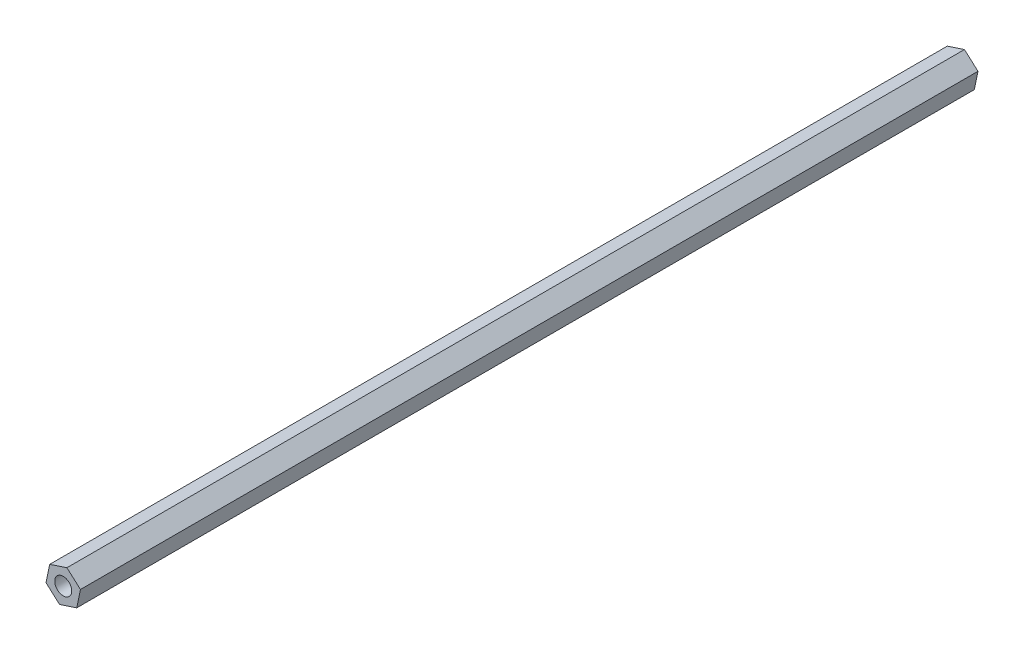
SolidWorks part; units mm, degrees
ref_plane "Alzado" through (0, 0, 0) normal (0, 0, 1) x (1, 0, 0)
ref_plane "Planta" through (0, 0, 0) normal (0, 1, 0) x (1, 0, 0)
ref_plane "Vista lateral" through (0, 0, 0) normal (1, 0, 0) x (0, 0, -1)
sketch "Croquis1" plane through (0, 0, 0) normal (0, 0, 1) x (1, 0, 0)
  line L1 (3.454, 1.14) -> (0.7397, 3.5613)
  line L2 (0.7397, 3.5613) -> (-2.7143, 2.4213)
  line L3 (-2.7143, 2.4213) -> (-3.454, -1.14)
  line L4 (-3.454, -1.14) -> (-0.7397, -3.5613)
  line L5 (-0.7397, -3.5613) -> (2.7143, -2.4213)
  line L6 (2.7143, -2.4213) -> (3.454, 1.14)
  circle A0 centre (0, 0) radius 3.15 construction
  dimension "D1" = 6.3
extrude "Saliente-Extruir1" add sketch "Croquis1" along normal blind 180
sketch "Croquis2" plane through (0, 0, 180) normal (0, 0, 1) x (1, 0, 0)
  circle A0 centre (0, 0) radius 1.7
  dimension "D1" = 3.4
extrude "Cortar-Extruir1" cut sketch "Croquis2" against normal through all
